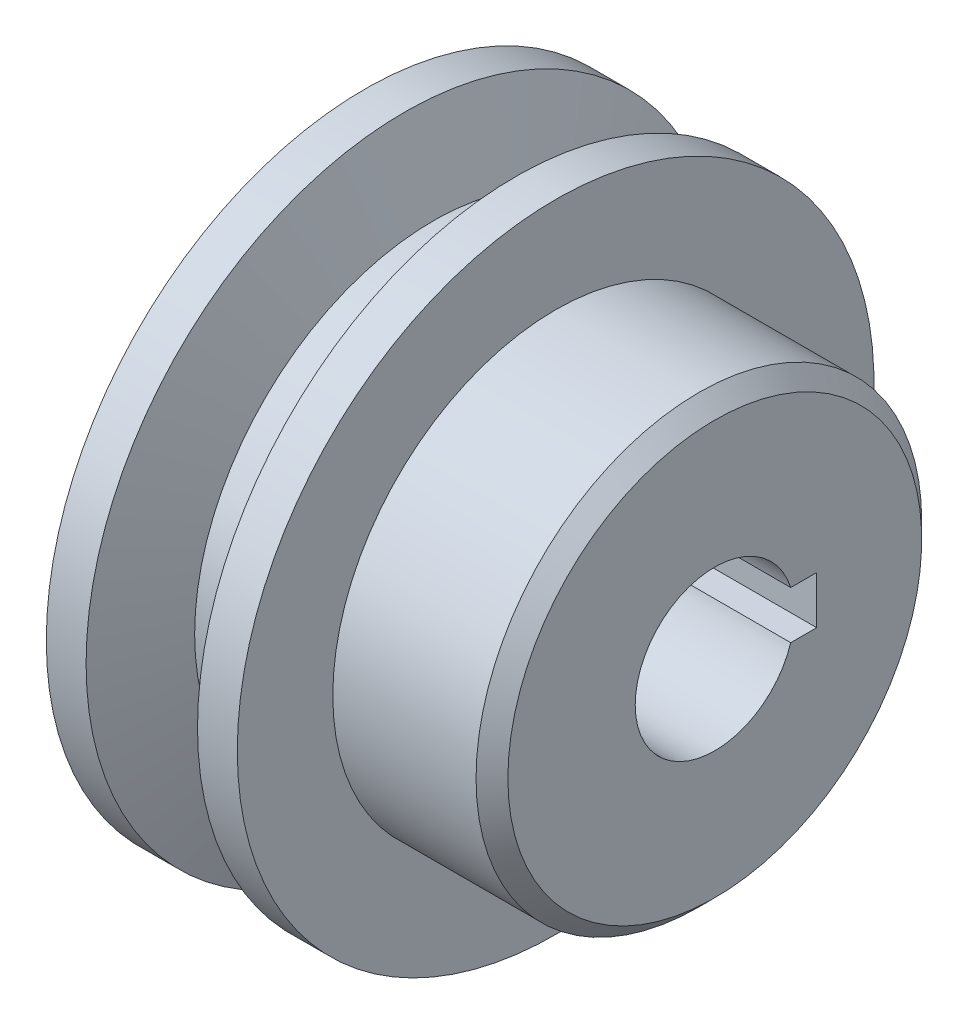
SolidWorks part; units mm, degrees
ref_plane "Front Plane" through (0, 0, 0) normal (0, 0, 1) x (1, 0, 0)
ref_plane "Top Plane" through (0, 0, 0) normal (0, 1, 0) x (1, 0, 0)
ref_plane "Right Plane" through (0, 0, 0) normal (1, 0, 0) x (0, 0, -1)
sketch "Sketch2" plane through (0, 0, 0) normal (0, 0, 1) x (1, 0, 0)
  line L0 (0, 0) -> (22, 0)
  line L1 (22, 0) -> (22, 14)
  line L2 (22, 14) -> (12, 14)
  line L3 (12, 14) -> (12, 20)
  line L4 (12, 20) -> (9.5, 20)
  line L5 (9.5, 20) -> (7.6801, 15)
  line L6 (7.6801, 15) -> (4.3199, 15)
  line L7 (4.3199, 15) -> (2.5, 20)
  line L8 (2.5, 20) -> (0, 20)
  line L9 (0, 20) -> (0, 0)
  point P3 (0, 0)
  dimension "D1" = 22
  dimension "D2" = 14
  dimension "D3" = 6
  dimension "D4" = 20
  dimension "D5" = 10
  dimension "D6" = 12
  dimension "D7" = 7
  dimension "D8" = 40
  dimension "D9" = 15
revolve "Revolve1" add sketch "Sketch2" angle 360 about L0
sketch "Sketch3" plane through (22, 0, 0) normal (1, 0, 0) x (0, 0, -1)
  line L0 (-20, 0) -> (5.226, 0) construction
  line L1 (0, 20) -> (0, -20) construction
  line L2 (6.4, 1.5) -> (6.4, -1.5)
  line L3 (6.4, 1.5) -> (4.7697, 1.5)
  line L4 (6.4, -1.5) -> (4.7697, -1.5)
  arc A0 (4.7697, 1.5) -> (4.7697, -1.5) centre (0, 0) ccw
  circle A1 centre (0, 0) radius 20 construction
  point P12 (6.4, 0)
  dimension "D1" = 10
  dimension "D2" = 6.4
  dimension "D3" = 3
extrude "Cut-Extrude1" cut sketch "Sketch3" against normal through all
chamfer "Chamfer1" distance 1 angle 45 1 edges at (22, 0, 14)
